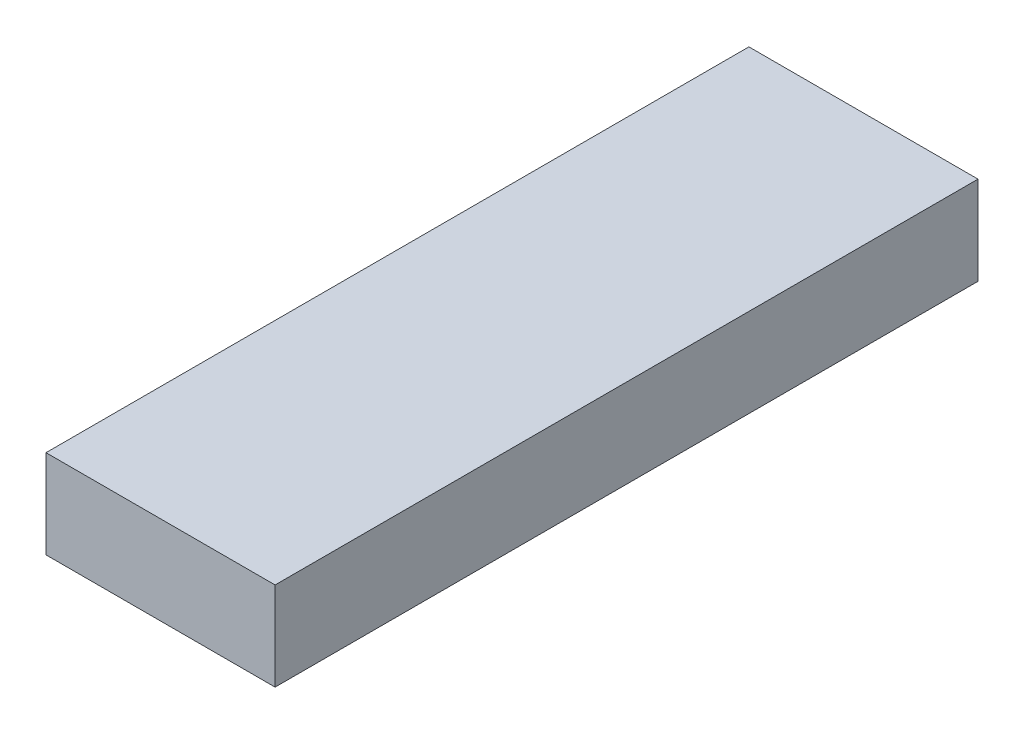
SolidWorks part; units mm, degrees
ref_plane "Front Plane" through (0, 0, 0) normal (0, 0, 1) x (1, 0, 0)
ref_plane "Top Plane" through (0, 0, 0) normal (0, 1, 0) x (1, 0, 0)
ref_plane "Right Plane" through (0, 0, 0) normal (1, 0, 0) x (0, 0, -1)
sketch "Sketch1" plane through (0, 0, 0) normal (0, 1, 0) x (1, 0, 0)
  line L1 (0, 0) -> (44, 0)
  line L2 (0, 0) -> (0, 135)
  line L3 (0, 135) -> (44, 135)
  line L4 (44, 0) -> (44, 135)
  dimension "D1" = 135
  dimension "D2" = 44
extrude "Boss-Extrude1" add sketch "Sketch1" along normal blind 17
